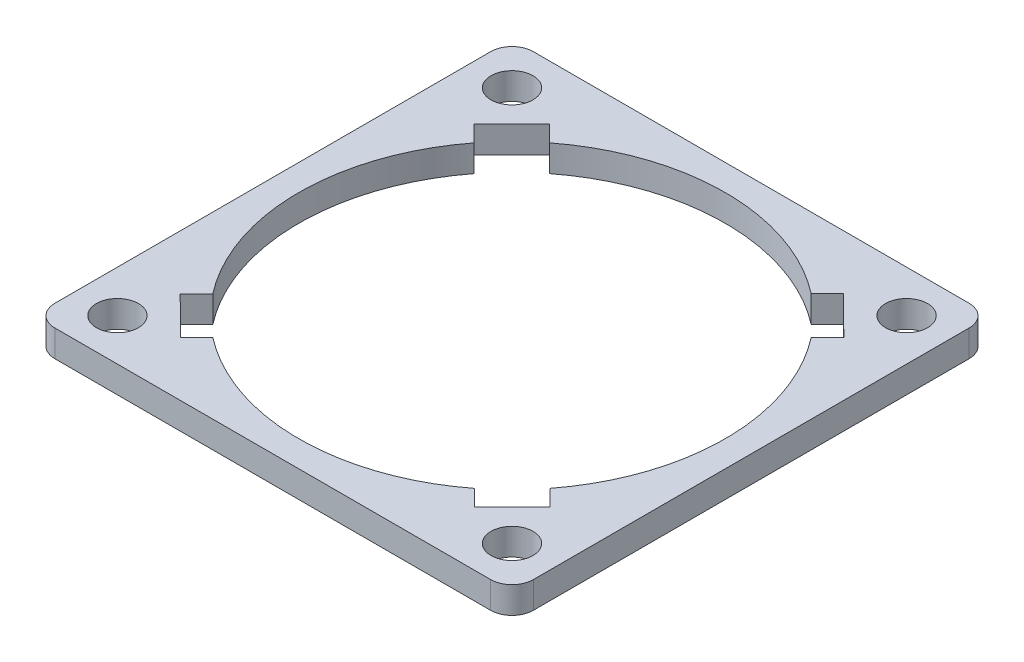
SolidWorks part; units mm, degrees
ref_plane "Front Plane" through (0, 0, 0) normal (0, 0, 1) x (1, 0, 0)
ref_plane "Top Plane" through (0, 0, 0) normal (0, 1, 0) x (1, 0, 0)
ref_plane "Right Plane" through (0, 0, 0) normal (1, 0, 0) x (0, 0, -1)
sketch "Sketch1" plane through (0, 0, 0) normal (0, 1, 0) x (1, 0, 0)
  line L0 (-13.9933, 28.5) -> (-25.96, 28.5)
  line L1 (25.96, -28.5) -> (13.9933, -28.5)
  line L2 (28.5, -25.96) -> (28.5, -13.9933)
  line L3 (25.96, 28.5) -> (13.9933, 28.5)
  line L4 (-28.5, -25.96) -> (-28.5, -13.9933)
  line L5 (28.5, -28.5) -> (19.7566, -19.7566) construction
  line L6 (28.5, 28.5) -> (19.7566, 19.7566) construction
  line L7 (28.5, 13.9933) -> (28.5, 25.96)
  line L8 (-13.9933, -28.5) -> (-25.96, -28.5)
  line L9 (-28.5, 13.9933) -> (-28.5, 25.96)
  line L10 (-28.5, 13.9933) -> (-28.5, -13.9933)
  line L11 (-13.9933, 28.5) -> (13.9933, 28.5)
  line L12 (28.5, 13.9933) -> (28.5, -13.9933)
  line L13 (13.9933, -28.5) -> (-13.9933, -28.5)
  line L14 (17.5258, -21.9902) -> (15.5876, -20.0546)
  line L15 (17.5258, -21.9902) -> (22.013, -17.4972)
  line L16 (-22.013, 17.4972) -> (-17.5258, 21.9902)
  line L17 (22.013, -17.4972) -> (20.0748, -15.5615)
  line L20 (-21.9902, -17.5258) -> (-20.0546, -15.5876)
  line L21 (-21.9902, -17.5258) -> (-17.4972, -22.013)
  line L22 (-17.4972, -22.013) -> (-15.5615, -20.0748)
  line L23 (17.4972, 22.013) -> (21.9902, 17.5258)
  line L24 (15.5615, 20.0748) -> (17.4972, 22.013)
  line L25 (20.0546, 15.5876) -> (21.9902, 17.5258)
  line L26 (-20.0748, 15.5615) -> (-22.013, 17.4972)
  line L27 (-15.5876, 20.0546) -> (-17.5258, 21.9902)
  line L32 (-19.7566, 19.7566) -> (-28.5, 28.5) construction
  line L34 (-19.7566, -19.7566) -> (-28.5, -28.5) construction
  arc A0 (15.5615, 20.0748) -> (-15.5876, 20.0546) centre (0, 0) ccw
  arc A5 (-25.96, -28.5) -> (-28.5, -25.96) centre (-25.96, -25.96) cw
  arc A6 (25.96, -28.5) -> (28.5, -25.96) centre (25.96, -25.96) ccw
  arc A7 (28.5, 25.96) -> (25.96, 28.5) centre (25.96, 25.96) ccw
  arc A8 (-25.96, 28.5) -> (-28.5, 25.96) centre (-25.96, 25.96) ccw
  circle A9 centre (-23.5, 23.5) radius 2.5
  circle A10 centre (23.5, 23.5) radius 2.5
  circle A11 centre (23.5, -23.5) radius 2.5
  circle A12 centre (-23.5, -23.5) radius 2.5
  arc A13 (-20.0748, 15.5615) -> (-20.0546, -15.5876) centre (0, 0) ccw
  arc A14 (-15.5615, -20.0748) -> (15.5876, -20.0546) centre (0, 0) ccw
  arc A15 (20.0748, -15.5615) -> (20.0546, 15.5876) centre (0, 0) ccw
  point P38 (0, 0)
  point P46 (0, 0)
  dimension "D1" = 6.35
  dimension "D4" = 2.54
  dimension "D5" = 50.8
  dimension "D6" = 5
  dimension "D2" = 57
  dimension "D3" = 57
  dimension "D7" = 5
  dimension "D9" = 27.94
  dimension "D8" = 4
  dimension "D10" = 2
extrude "Boss-Extrude1" add sketch "Sketch1" along normal blind 3.175
